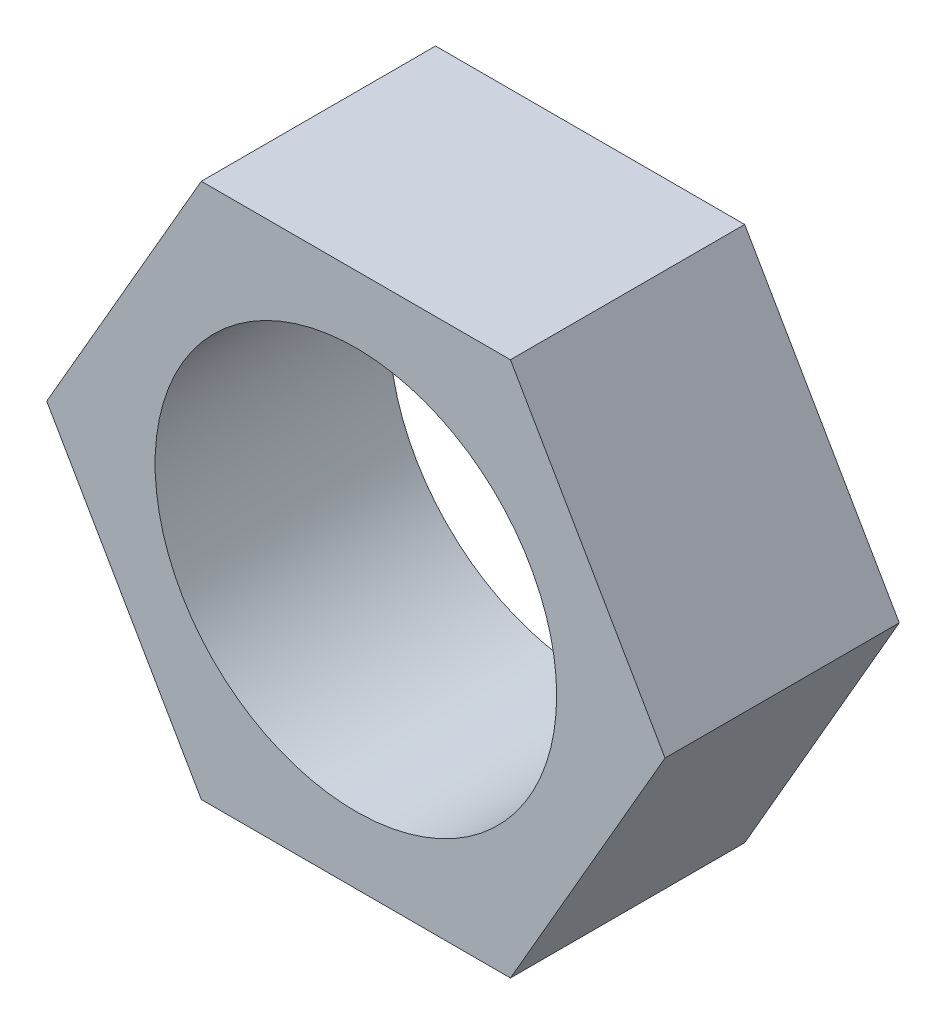
SolidWorks part; units mm, degrees
ref_plane "Alzado" through (0, 0, 0) normal (0, 0, 1) x (1, 0, 0)
ref_plane "Planta" through (0, 0, 0) normal (0, 1, 0) x (1, 0, 0)
ref_plane "Vista lateral" through (0, 0, 0) normal (1, 0, 0) x (0, 0, -1)
sketch "Croquis1" plane through (0, 0, 0) normal (0, 0, 1) x (1, 0, 0)
  line L1 (9.2376, 0) -> (4.6188, 8)
  line L2 (4.6188, 8) -> (-4.6188, 8)
  line L3 (-4.6188, 8) -> (-9.2376, 0)
  line L4 (-9.2376, 0) -> (-4.6188, -8)
  line L5 (-4.6188, -8) -> (4.6188, -8)
  line L6 (4.6188, -8) -> (9.2376, 0)
  circle A0 centre (0, 0) radius 8 construction
  circle A1 centre (0, 0) radius 6
  dimension "D1" = 16
  dimension "D2" = 12
extrude "Saliente-Extruir1" add sketch "Croquis1" along normal blind 7
